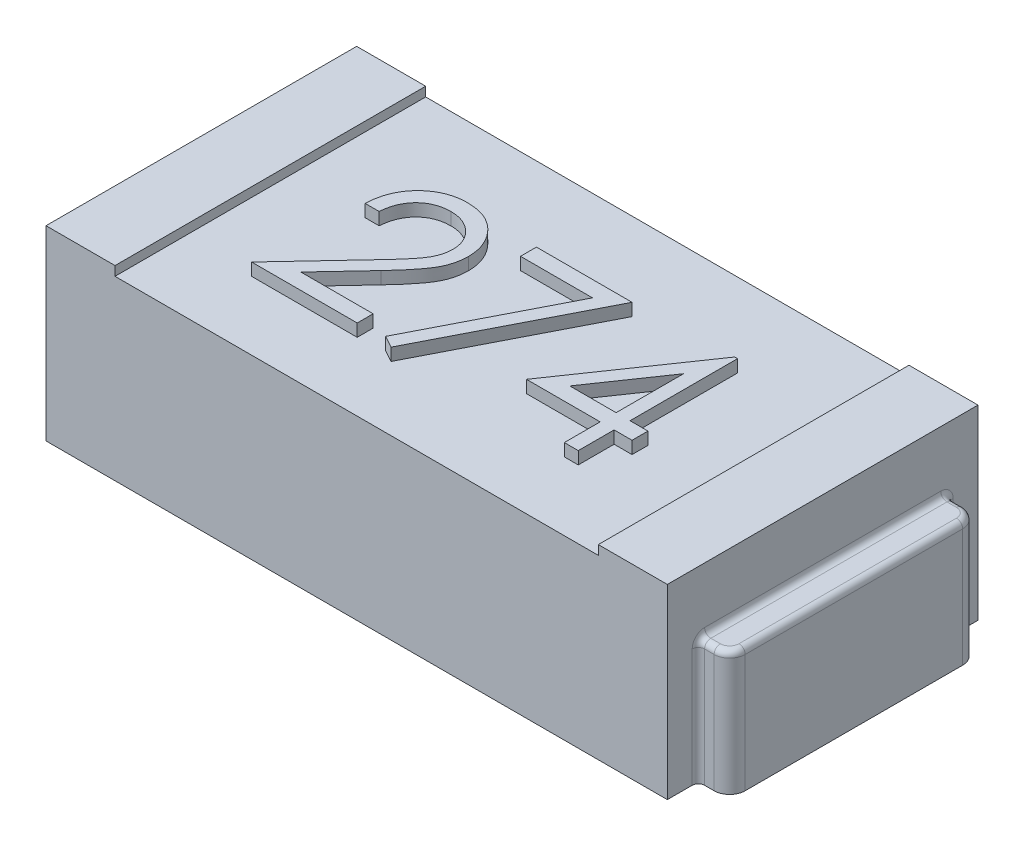
SolidWorks part; units mm, degrees
ref_plane "Plan de face" through (0, 0, 0) normal (0, 0, 1) x (1, 0, 0)
ref_plane "Plan de dessus" through (0, 0, 0) normal (0, 1, 0) x (1, 0, 0)
ref_plane "Plan de droite" through (0, 0, 0) normal (1, 0, 0) x (0, 0, -1)
sketch "Esquisse1" plane through (0, 0, 0) normal (0, 1, 0) x (1, 0, 0)
  line L1 (1, -0.5) -> (-1, -0.5)
  line L2 (1, -0.5) -> (1, 0.5)
  line L3 (1, 0.5) -> (-1, 0.5)
  line L4 (-1, -0.5) -> (-1, 0.5)
  line L5 (1, -0.5) -> (-1, 0.5) construction
  line L6 (1, 0.5) -> (-1, -0.5) construction
  point P0 (0, 0)
  dimension "D1" = 2
  dimension "D2" = 1
extrude "Boss.-Extru.1" add sketch "Esquisse1" along normal blind 0.6
sketch "Esquisse2" plane through (0, 0.6, 0) normal (0, 1, 0) x (1, 0, 0)
  line L0 (1, 0.5) -> (-1, 0.5) construction
  line L1 (0.7778, -0.5) -> (-0.7778, -0.5)
  line L2 (0.7778, -0.5) -> (0.7778, 0.5)
  line L3 (0.7778, 0.5) -> (-0.7778, 0.5)
  line L4 (-0.7778, -0.5) -> (-0.7778, 0.5)
  line L5 (0.7778, -0.5) -> (-0.7778, 0.5) construction
  line L6 (0.7778, 0.5) -> (-0.7778, -0.5) construction
  point P0 (0, 0)
extrude "Enlèv. mat.-Extru.1" cut sketch "Esquisse2" against normal blind 0.03
sketch "Esquisse3" plane through (0, 0, 0) normal (0, 1, 0) x (1, 0, 0)
  line L1 (1, 0.4) -> (1.0506, 0.4)
  line L2 (1, 0.4) -> (1, -0.4)
  line L3 (1, -0.4) -> (1.0506, -0.4)
  line L4 (1.1006, 0.35) -> (1.1006, -0.35)
  line L8 (1, -0.5) -> (1, 0.5) construction
  arc A0 (1.0506, -0.4) -> (1.1006, -0.35) centre (1.0506, -0.35) ccw
  arc A1 (1.0506, 0.4) -> (1.1006, 0.35) centre (1.0506, 0.35) cw
  dimension "D1" = 0.05
  dimension "D2" = 0.8
  dimension "D3" = 0.1006
extrude "Boss.-Extru.2" add sketch "Esquisse3" along normal blind 0.4
fillet "Congé1" radius 0.02 8 edges at (1, 0.2, -0.4) (1, 0.2, 0.4) (1.0253, 0.4, -0.4) (1.0859, 0.4, -0.3854) (1.1006, 0.4, 0) (1.0859, 0.4, 0.3854) (1.0253, 0.4, 0.4) (1, 0.4, 0)
mirror "Symétrie2" about plane through (0, 0, 0) normal (1, 0, 0) of "Congé1", "Boss.-Extru.2"
sketch "Esquisse4" plane through (0, 0.57, 0) normal (0, 1, 0) x (1, 0, 0)
  line L0 (0.7576, -0.2803) -> (-0.7576, -0.2803) construction
  text T0 "274\r\n" font "Century Gothic" height 0.5
  point P3 (0, -0.2803)
extrude "Boss.-Extru.3" add sketch "Esquisse4" along normal blind 0.04
